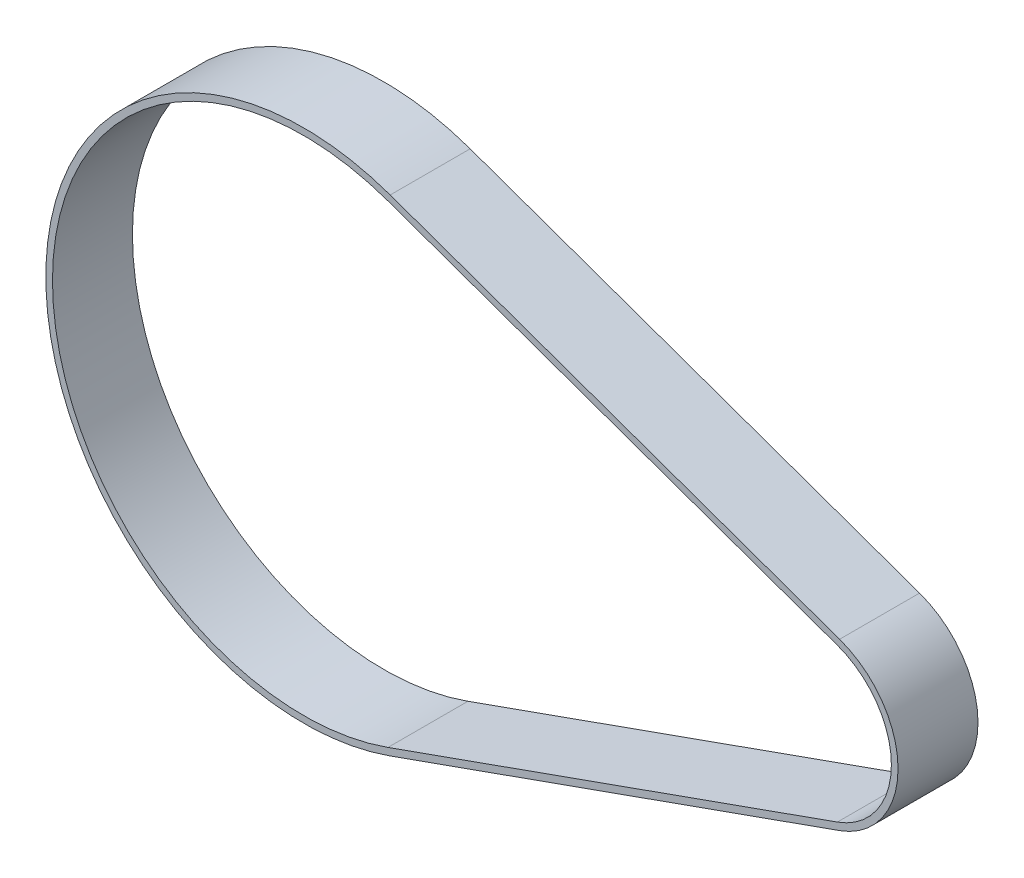
SolidWorks part; units mm, degrees
material "Caucho"
ref_plane "Alzado" through (0, 0, 0) normal (0, 0, 1) x (1, 0, 0)
ref_plane "Planta" through (0, 0, 0) normal (0, 1, 0) x (1, 0, 0)
ref_plane "Vista lateral" through (0, 0, 0) normal (1, 0, 0) x (0, 0, -1)
sketch "Croquis1" plane through (0, 0, 0) normal (0, 0, 1) x (1, 0, 0)
  line L0 (6.3247, 17.7573) -> (40.0467, 5.7464)
  line L1 (0, 0) -> (79.1587, 0) construction
  line L2 (40.0467, -5.7464) -> (6.3247, -17.7573)
  line L3 (40.2145, -6.2174) -> (6.4924, -18.2283)
  line L4 (6.4924, 18.2283) -> (40.2145, 6.2174)
  arc A0 (6.3247, 17.7573) -> (6.3247, -17.7573) centre (0, 0) ccw
  arc A1 (40.0467, -5.7464) -> (40.0467, 5.7464) centre (38, 0) ccw
  arc A2 (6.4924, 18.2283) -> (6.4924, -18.2283) centre (0, 0) ccw
  arc A3 (40.2145, -6.2174) -> (40.2145, 6.2174) centre (38, 0) ccw
  dimension "D1" = 12.2
  dimension "D2" = 37.7
  dimension "D3" = 38
  dimension "D4" = 0.5
extrude "Saliente-Extruir1" add sketch "Croquis1" along normal blind 6
